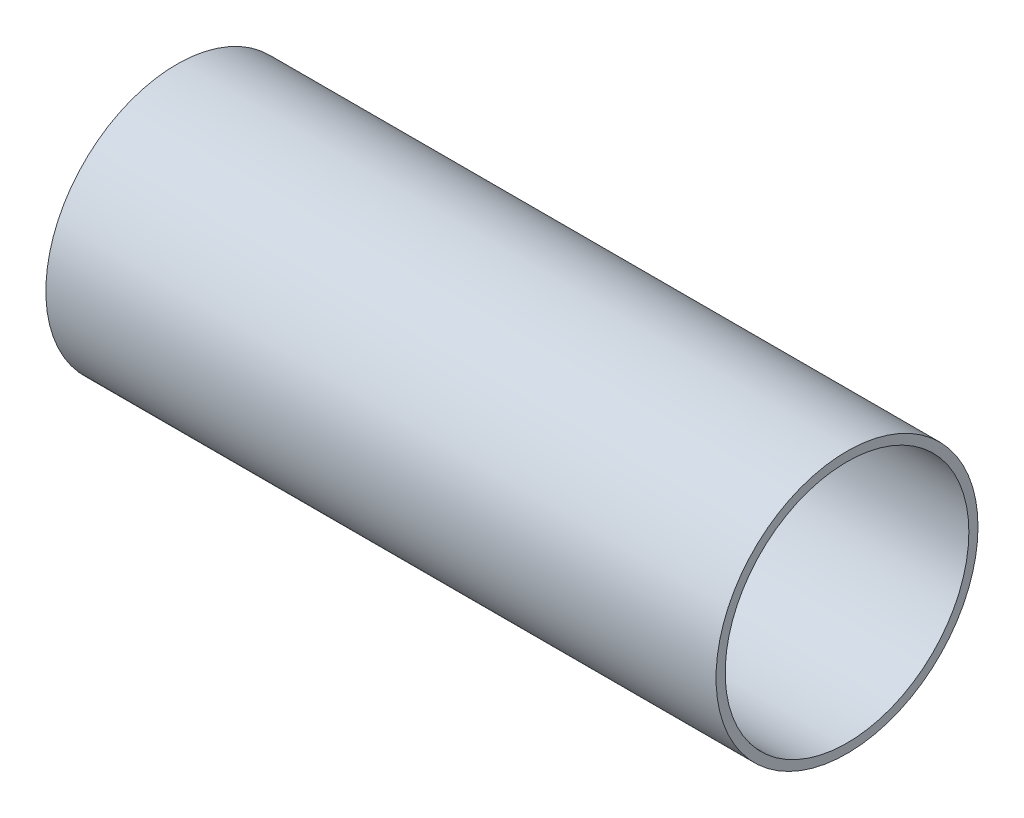
SolidWorks part; units mm, degrees
material "Wildman Fiberglass"
ref_plane "Front Plane" through (0, 0, 0) normal (0, 0, 1) x (1, 0, 0)
ref_plane "Top Plane" through (0, 0, 0) normal (0, 1, 0) x (1, 0, 0)
ref_plane "Right Plane" through (0, 0, 0) normal (1, 0, 0) x (0, 0, -1)
sketch "Sketch1" plane through (0, 0, 0) normal (1, 0, 0) x (0, 0, -1)
  circle A0 centre (0, 0) radius 27.305
  circle A1 centre (0, 0) radius 25.4
  dimension "D1" = 50.8
  dimension "D2" = 54.61
extrude "Boss-Extrude1" add sketch "Sketch1" along normal mid plane 139.7
